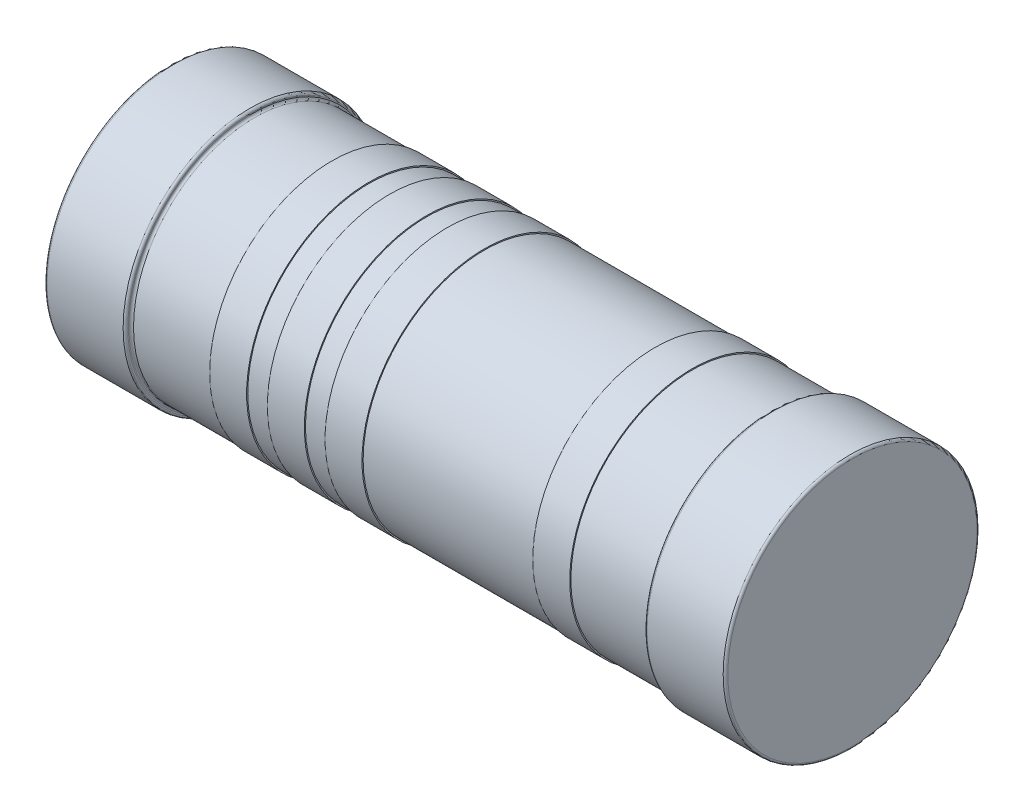
SolidWorks part; units mm, degrees
ref_plane "Front Plane" through (0, 0, 0) normal (0, 0, 1) x (1, 0, 0)
ref_plane "Top Plane" through (0, 0, 0) normal (0, 1, 0) x (1, 0, 0)
ref_plane "Right Plane" through (0, 0, 0) normal (1, 0, 0) x (0, 0, -1)
sketch "Sketch1" plane through (0, 0, 0) normal (0, 0, 1) x (1, 0, 0)
  line L0 (-2.95, 1.1) -> (2.95, 1.1)
  line L1 (0, 0) -> (0, 1.1) construction
  line L2 (-2.95, 1.1) -> (-3.0256, 1.1) construction
  line L3 (2.95, 1.1) -> (2.95, 0.02)
  line L4 (-2.93, 0) -> (-2.27, 0)
  line L5 (-2.95, 0.02) -> (-2.95, 1.1)
  line L6 (-2.25, 0.02) -> (-2.25, 0.03)
  line L7 (-2.23, 0.05) -> (-1.56, 0.05)
  line L8 (2.25, 0.03) -> (2.25, 0.02)
  line L9 (2.27, 0) -> (2.93, 0)
  line L10 (-1.56, 0.05) -> (-1.56, 0.04)
  line L11 (-1.56, 0.04) -> (-1.24, 0.04)
  line L12 (-1.24, 0.04) -> (-1.24, 0.05)
  line L13 (-1.06, 0.05) -> (-1.06, 0.04)
  line L14 (-1.06, 0.04) -> (-0.74, 0.04)
  line L15 (-0.74, 0.04) -> (-0.74, 0.05)
  line L16 (-0.24, 0.04) -> (-0.56, 0.04)
  line L17 (-0.56, 0.04) -> (-0.56, 0.05)
  line L18 (1.56, 0.05) -> (2.23, 0.05)
  line L19 (-0.24, 0.04) -> (-0.24, 0.05)
  line L20 (1.56, 0.05) -> (1.56, 0.04)
  line L21 (1.56, 0.04) -> (1.24, 0.04)
  line L22 (1.24, 0.04) -> (1.24, 0.05)
  line L23 (-1.4, 0.04) -> (-1.4, -0.0114) construction
  line L24 (-0.9, 0.04) -> (-0.9, -0.0114) construction
  line L25 (-0.4, 0.04) -> (-0.4, -0.0151) construction
  line L26 (1.4, 0.04) -> (1.4, -0.0151) construction
  line L27 (-0.24, 0.05) -> (1.24, 0.05)
  line L28 (-0.74, 0.05) -> (-0.56, 0.05)
  line L29 (-1.24, 0.05) -> (-1.06, 0.05)
  arc A0 (2.95, 0.02) -> (2.93, 0) centre (2.93, 0.02) cw
  arc A1 (2.27, 0) -> (2.25, 0.02) centre (2.27, 0.02) cw
  arc A2 (2.25, 0.03) -> (2.23, 0.05) centre (2.23, 0.03) ccw
  arc A3 (-2.23, 0.05) -> (-2.25, 0.03) centre (-2.23, 0.03) ccw
  arc A4 (-2.25, 0.02) -> (-2.27, 0) centre (-2.27, 0.02) cw
  arc A5 (-2.95, 0.02) -> (-2.93, 0) centre (-2.93, 0.02) ccw
  point P15 (2.95, 0)
  point P18 (2.25, 0)
  dimension "D5" = 0.02
  dimension "D1" = 5.9
  dimension "D2" = 0.7
  dimension "D3" = 0.05
  dimension "D4" = 1.1
  dimension "D6" = 0.32
  dimension "D7" = 0.01
  dimension "D8" = 0.5
  dimension "D9" = 0.5
  dimension "D10" = 0.4
  dimension "D11" = 1.4
revolve "Revolve1" add sketch "Sketch1" angle 360 about L2
